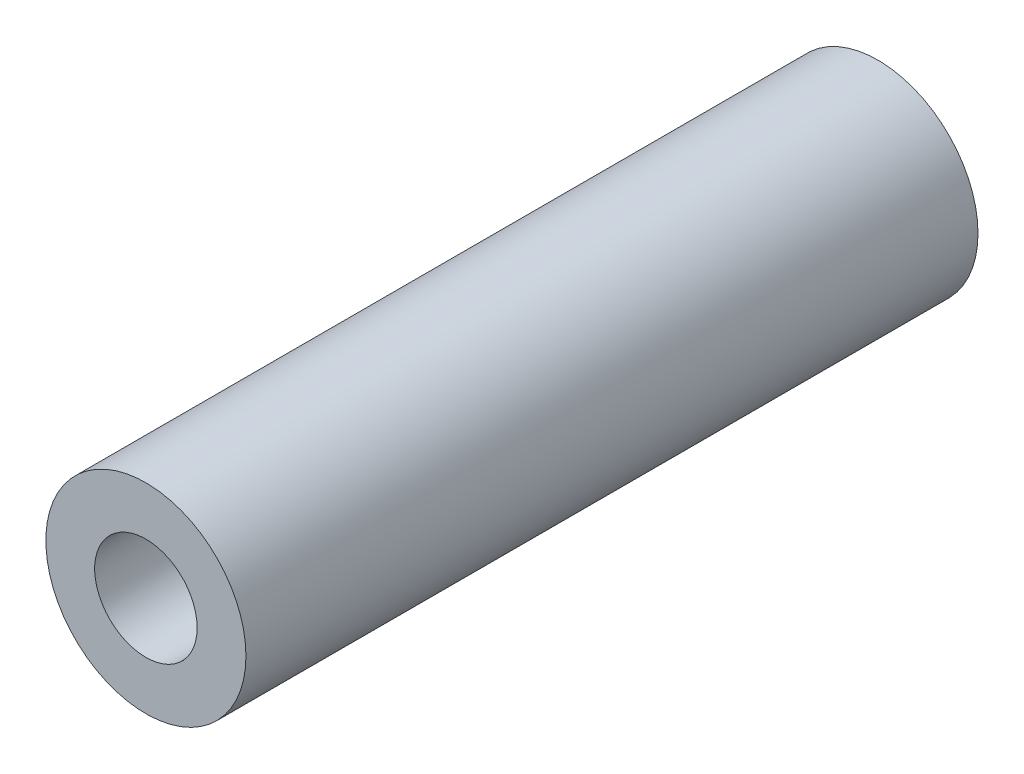
SolidWorks part; units mm, degrees
ref_plane "正面" through (0, 0, 0) normal (1, 0, 0) x (0, 1, 0)
ref_plane "平面" through (0, 0, 0) normal (0, 0, 1) x (0, 1, 0)
ref_plane "右側面" through (0, 0, 0) normal (0, 1, 0) x (-1, 0, 0)
sketch "ｽｹｯﾁ1" plane through (0, 0, 0) normal (0, 0, 1) x (0, 1, 0)
  circle A0 centre (0, 0) radius 2.1
  circle A1 centre (0, 0) radius 4.1
  circle A2 centre (0, 0) radius 0.1
  point P3 (0, 0)
  dimension "D1" = 4.2
  dimension "D2" = 2
  dimension "D3" = 2
extrude "ﾎﾞｽ - 押し出し1" add sketch "ｽｹｯﾁ1" along normal blind 30 contours A1 A0
